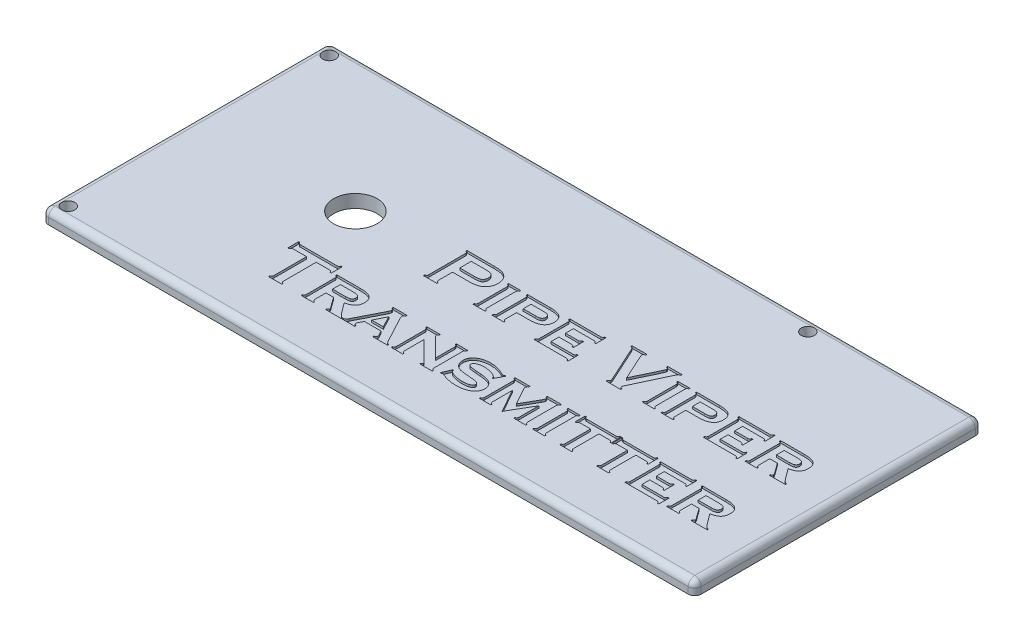
SolidWorks part; units mm, degrees
ref_plane "Front Plane" through (0, 0, 0) normal (0, 0, 1) x (1, 0, 0)
ref_plane "Top Plane" through (0, 0, 0) normal (0, 1, 0) x (1, 0, 0)
ref_plane "Right Plane" through (0, 0, 0) normal (1, 0, 0) x (0, 0, -1)
sketch "Sketch1" plane through (0, 0, 0) normal (0, 1, 0) x (1, 0, 0)
  line L1 (-75, -33) -> (75, -33)
  line L2 (-75, -33) -> (-75, 33)
  line L3 (-75, 33) -> (75, 33)
  line L4 (75, -33) -> (75, 33)
  line L5 (-75, -33) -> (75, 33) construction
  line L6 (-75, 33) -> (75, -33) construction
  point P0 (0, 0)
  dimension "D1" = 66
  dimension "D2" = 150
extrude "Boss-Extrude1" add sketch "Sketch1" along normal blind 3
fillet "Fillet1" radius 1.5 8 edges at (0, 3, 33) (-75, 3, 0) (0, 3, -33) (75, 3, 0) (75, 1.5, -33) (75, 1.5, 33) (-75, 1.5, -33) (-75, 1.5, 33)
sketch "Sketch2" plane through (0, 0, 0) normal (0, -1, 0) x (1, 0, 0)
  circle A0 centre (-72, 30) radius 1.5 construction
  circle A1 centre (-72, 30) radius 1.5
  circle A2 centre (-72, -30) radius 1.5 construction
  circle A3 centre (-72, -30) radius 1.5
  circle A4 centre (38, -30) radius 1.5 construction
  circle A5 centre (38, -30) radius 1.5
extrude "Cut-Extrude1" cut sketch "Sketch2" against normal through all both and the other way through all
sketch "Sketch3" plane through (0, 3, 0) normal (0, 1, 0) x (1, 0, 0)
  line L0 (38, 30) -> (38, -26) construction
  line L1 (38, 30) -> (38, -26) construction
  line L2 (-72, 30) -> (38, 30) construction
  line L3 (-72, 30) -> (38, 30) construction
  circle A0 centre (-38, 2) radius 5
  dimension "D3" = 10
  dimension "D1" = 76
  dimension "D2" = 28
extrude "Cut-Extrude2" cut sketch "Sketch3" against normal through all both
sketch "Sketch4" plane through (0, 3, 0) normal (0, 1, 0) x (1, 0, 0)
  line L0 (-73.5, -3) -> (73.5, -3) construction
  line L1 (-73.5, 30) -> (-73.5, -30) construction
  line L2 (73.5, -31.5) -> (73.5, 31.5) construction
  line L4 (-73.5, -21) -> (73.5, -21) construction
  circle A0 centre (-38, 2) radius 5 construction
  text T0 "  Pipe Viper  " font "Copperplate Gothic Bold" height 10
  text T1 "Transmitter  " font "Copperplate Gothic Bold" height 10
  dimension "D1" = 18
extrude "Cut-Extrude3" cut sketch "Sketch4" against normal blind 0.5
